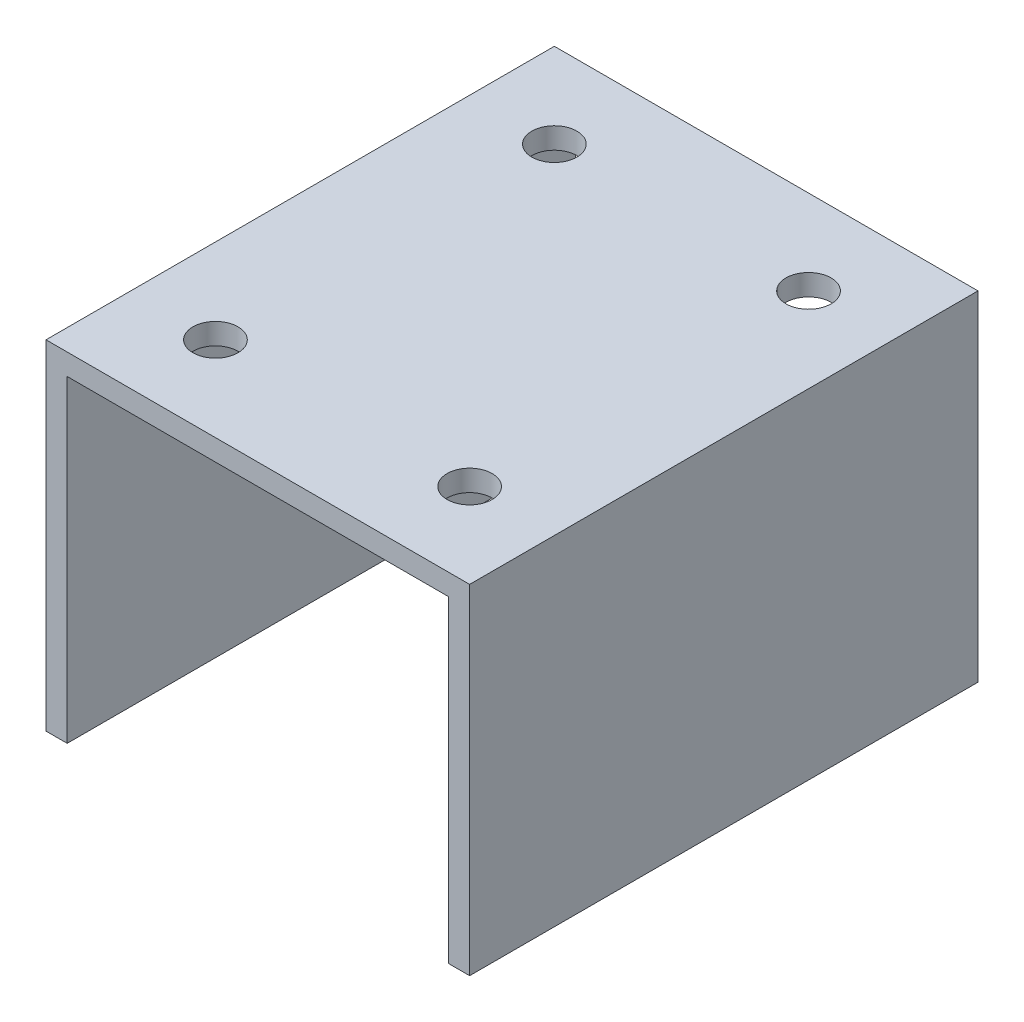
SolidWorks part; units mm, degrees
ref_plane "Front Plane" through (0, 0, 0) normal (0, 0, 1) x (1, 0, 0)
ref_plane "Top Plane" through (0, 0, 0) normal (0, 1, 0) x (1, 0, 0)
ref_plane "Right Plane" through (0, 0, 0) normal (1, 0, 0) x (0, 0, -1)
sketch "Sketch1" plane through (0, 0, 0) normal (0, 0, 1) x (1, 0, 0)
  line L0 (28.575, -47.625) -> (31.75, -47.625)
  line L1 (-31.75, 3.175) -> (31.75, 3.175)
  line L2 (-31.75, 3.175) -> (-31.75, -47.625)
  line L3 (-31.75, -47.625) -> (-28.575, -47.625)
  line L4 (31.75, 3.175) -> (31.75, -47.625)
  line L6 (-28.575, -47.625) -> (-28.575, 0)
  line L7 (-28.575, 0) -> (28.575, 0)
  line L8 (28.575, -47.625) -> (28.575, 0)
  dimension "D1" = 3.175
  dimension "D2" = 63.5
  dimension "D3" = 50.8
  dimension "D4" = 3.175
extrude "Boss-Extrude1" add sketch "Sketch1" along normal mid plane 76.2
hole_wizard "1/4 Clearance Hole1" positions "Sketch3" profile "Sketch2" hole size "1/4" standard "ANSI Inch" end condition through all
sketch "Sketch3" plane through (0, 3.175, 0) normal (0, 1, 0) x (1, 0, 0)
  line L2 (-19.05, 25.4) -> (19.05, 25.4)
  line L3 (-19.05, 25.4) -> (-19.05, -25.4)
  line L4 (-19.05, -25.4) -> (19.05, -25.4)
  line L5 (19.05, 25.4) -> (19.05, -25.4)
  line L6 (19.05, 25.4) -> (-19.05, -25.4) construction
  point P61 (-19.05, 25.4)
  point P64 (19.05, 25.4)
  point P67 (19.05, -25.4)
  point P70 (-19.05, -25.4)
  dimension "D1" = 38.1
  dimension "D2" = 50.8
sketch "Sketch2" plane through (-19.05, 3.175, -25.4) normal (1, 0, 0) x (0, 0, 1)
  line L0 (0, 0) -> (0, 50.8)
  line L1 (0, 50.8) -> (3.3782, 50.8)
  line L2 (3.3782, 50.8) -> (3.3782, 0)
  line L5 (3.3782, 0) -> (0, 0)
  line L11 (0, -6.35) -> (0, 107.95) construction
  dimension "Thru Hole Dia." = 6.7564
  dimension "Thru Hole Depth" = 50.8
